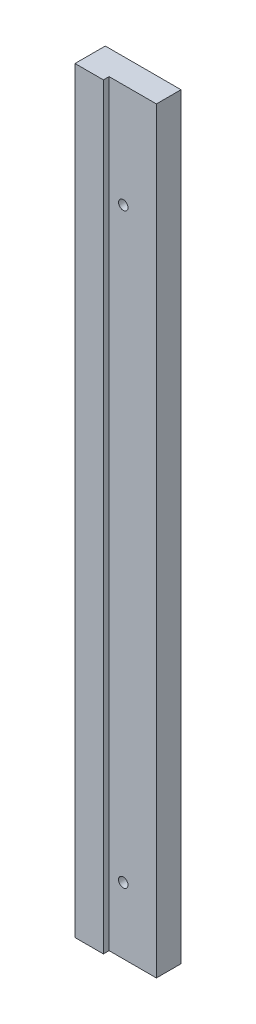
SolidWorks part; units mm, degrees
material "Литая легированная сталь"
ref_plane "Front" through (0, 0, 0) normal (0, 0, 1) x (1, 0, 0)
ref_plane "Top" through (0, 0, 0) normal (0, 1, 0) x (1, 0, 0)
ref_plane "Right" through (0, 0, 0) normal (1, 0, 0) x (0, 0, -1)
sketch "Sketch1" plane through (0, 0, 0) normal (0, 0, 1) x (1, 0, 0)
  line L1 (-20, 200) -> (20, 200)
  line L2 (-20, 200) -> (-20, -200)
  line L3 (-20, -200) -> (20, -200)
  line L4 (20, 200) -> (20, -200)
  line L5 (-20, 200) -> (20, -200) construction
  line L6 (-20, -200) -> (20, 200) construction
  point P0 (0, 0)
  dimension "D1" = 400
  dimension "D2" = 40
extrude "Extrude1" add sketch "Sketch1" along normal blind 16
sketch "Sketch2" plane through (0, -200, 0) normal (0, -1, 0) x (1, 0, 0)
  line L0 (-20, 16) -> (20, 16) construction
  line L1 (-5, 16) -> (20, 16)
  line L2 (-5, 16) -> (-5, 13)
  line L3 (-5, 13) -> (20, 13)
  line L4 (20, 16) -> (20, 13)
  line L5 (20, 16) -> (20, 0) construction
  dimension "D1" = 25
  dimension "D2" = 3
extrude "Extrude2" cut sketch "Sketch2" against normal up to next
hole_wizard "M6 Tapped Hole1" positions "Sketch5" profile "Sketch6" tap size "M6" standard "DIN" end condition through all
sketch "Sketch5" plane through (0, 0, 0) normal (0, 0, -1) x (-1, 0, 0)
  point P0 (-2.5, 145)
  point P3 (-2.5, -165)
sketch "Sketch6" plane through (2.5, 145, 0) normal (1, 0, 0) x (0, 1, 0)
  line L0 (0, 0) -> (0, 16)
  line L1 (0, 16) -> (2.5, 16)
  line L2 (2.5, 16) -> (2.5, 0)
  line L5 (2.5, 0) -> (0, 0)
  line L11 (0, -6.35) -> (0, 107.95) construction
  dimension "Диаметр проходного сверла" = 5
  dimension "Глубина проходного сверла" = 16
cosmetic thread "Cosmetic Thread8" parameters "D2"=6
cosmetic thread "Cosmetic Thread9" parameters "D2"=6
